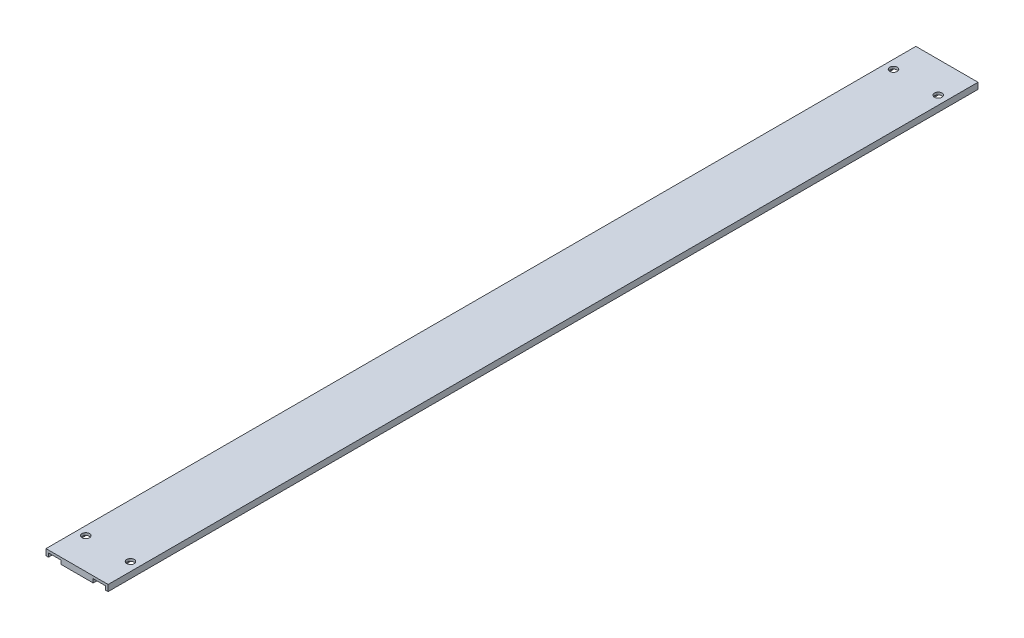
SolidWorks part; units mm, degrees
ref_plane "Front Plane" through (0, 0, 0) normal (0, 0, 1) x (1, 0, 0)
ref_plane "Top Plane" through (0, 0, 0) normal (0, 1, 0) x (1, 0, 0)
ref_plane "Right Plane" through (0, 0, 0) normal (1, 0, 0) x (0, 0, -1)
sketch "Sketch1" plane through (0, 0, 0) normal (0, 1, 0) x (1, 0, 0)
  line L0 (0, 0) -> (50, 0)
  line L1 (50, 0) -> (50, 700)
  line L2 (50, 700) -> (0, 700)
  line L3 (0, 700) -> (0, 0)
  dimension "D1" = 700
  dimension "D2" = 50
extrude "Boss-Extrude1" add sketch "Sketch1" along normal blind 5
sketch "Sketch6" plane through (0, 5, 0) normal (0, 1, 0) x (1, 0, 0)
  circle A0 centre (43, 25) radius 3
  circle A1 centre (7, 25) radius 3
  circle A2 centre (43, 675) radius 3
  circle A3 centre (7, 675) radius 3
extrude "Cut-Extrude3" cut sketch "Sketch6" against normal through all
sketch "Sketch11" plane through (0, 0, 0) normal (0, -1, 0) x (1, 0, 0)
  line L2 (12, 0) -> (12, -700)
  line L8 (2, -700) -> (2, 0)
  line L11 (2, 0) -> (12, 0)
  line L12 (12, -700) -> (2, -700)
  line L13 (38, -700) -> (48, -700)
  line L14 (38, 0) -> (48, 0)
  line L15 (38, 0) -> (38, -700)
  line L16 (48, 0) -> (48, -700)
extrude "Cut-Extrude4" cut sketch "Sketch11" against normal blind 3
